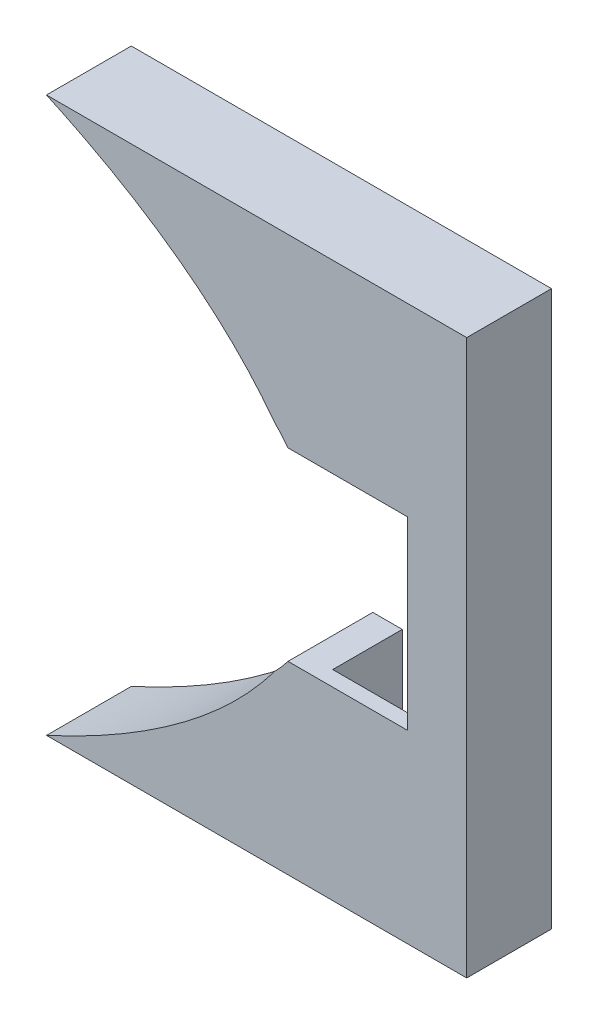
SolidWorks part; units mm, degrees
ref_plane "Front Plane" through (0, 0, 0) normal (0, 0, 1) x (1, 0, 0)
ref_plane "Top Plane" through (0, 0, 0) normal (0, 1, 0) x (1, 0, 0)
ref_plane "Right Plane" through (0, 0, 0) normal (1, 0, 0) x (0, 0, -1)
sketch "Sketch1" plane through (0, 0, 0) normal (0, 0, 1) x (1, 0, 0)
  line L0 (61.5951, 0) -> (57.3248, 0) construction
  line L1 (-2.6813, 23.8497) -> (-2.6813, -23.8497)
  line L2 (-2.6813, 23.8497) -> (-2.6813, -23.8497)
  line L3 (60.35, 4.95) -> (60.85, 4.95) construction
  line L4 (60.85, 5.45) -> (55.8, 5.45)
  line L5 (60.85, 5.45) -> (60.85, -5.45)
  line L6 (60.85, -5.45) -> (55.8, -5.45)
  line L7 (55.8, 5.45) -> (55.8, -5.45)
  line L8 (60.85, 5.45) -> (55.8, -5.45) construction
  line L9 (60.85, -5.45) -> (55.8, 5.45) construction
  line L10 (60.35, 4.95) -> (60.35, 5.45) construction
  line L11 (55.8, 5.45) -> (54.0622, 5.45)
  line L12 (55.8, -14.85) -> (63.1, 14.85) construction
  line L13 (63.1, 14.85) -> (64.6, 14.85) construction
  line L14 (54.3, -16.35) -> (64.6, -16.35)
  line L15 (54.3, -16.35) -> (54.3, 16.35)
  line L16 (54.3, 16.35) -> (64.6, 16.35)
  line L17 (64.6, -16.35) -> (64.6, 16.35)
  line L18 (54.3, -16.35) -> (64.6, 16.35) construction
  line L19 (54.3, 16.35) -> (64.6, -16.35) construction
  line L20 (63.1, 14.85) -> (63.1, 16.35) construction
  line L21 (54.3, 16.35) -> (39.8224, 16.35)
  line L22 (55.8, 14.85) -> (55.8, 4.95)
  line L23 (55.8, 4.95) -> (59.2, 4.95)
  line L24 (59.2, 4.95) -> (60.35, 4.95)
  line L25 (60.35, 4.95) -> (60.35, -4.95)
  line L26 (60.35, -4.95) -> (59.2, -4.95)
  line L27 (59.2, -4.95) -> (55.8, -4.95)
  line L28 (55.8, -4.95) -> (55.8, -14.85)
  line L29 (55.8, -14.85) -> (63.1, -14.85)
  line L30 (63.1, -14.85) -> (63.1, 14.85)
  line L31 (63.1, 14.85) -> (55.8, 14.85)
  line L32 (55.8, 14.85) -> (55.8, 4.95)
  line L33 (55.8, 4.95) -> (59.2, 4.95)
  line L34 (59.2, 4.95) -> (60.35, 4.95)
  line L35 (60.35, 4.95) -> (60.35, -4.95)
  line L36 (60.35, -4.95) -> (59.2, -4.95)
  line L37 (59.2, -4.95) -> (55.8, -4.95)
  line L38 (55.8, -4.95) -> (55.8, -14.85)
  line L39 (55.8, -14.85) -> (63.1, -14.85)
  line L40 (63.1, -14.85) -> (63.1, 14.85)
  line L41 (63.1, 14.85) -> (55.8, 14.85)
  line L42 (54.3, -16.35) -> (39.8224, -16.35)
  line L43 (55.8, -5.45) -> (54.0622, -5.45)
  line L44 (55.8, 4.95) -> (54.3, 4.95)
  line L45 (55.8, 4.95) -> (55.8, -4.95)
  line L46 (55.8, -4.95) -> (54.3, -4.95)
  line L47 (54.3, 4.95) -> (54.3, -4.95)
  arc A1 (53.264, -6.364) -> (53.264, 6.364) centre (46.9, 0) ccw
  arc A2 (53.264, -6.364) -> (53.264, 6.364) centre (46.9, 0) ccw
  spline S2 degree 3 poles (-2788.5351, -933.1128) (3254.9192, 628.8908) (-3260.7685, -317.1067) (2992.5839, 170.8336) knots -3.563477 -3.563477 -3.563477 -3.563477 4.61246 4.61246 4.61246 4.61246 only from (53.264, 6.364) to (-2.6813, 23.8497)
  spline S3 degree 3 poles (2992.541, -170.8303) (-3260.7166, 317.1006) (3254.8593, -628.8806) (-2788.4709, 933.0962) knots -3.612441 -3.612441 -3.612441 -3.612441 4.563448 4.563448 4.563448 4.563448 only from (-2.6813, -23.8497) to (53.264, -6.364)
  spline S4 degree 3 poles (53.264, 6.364) (41.9045, 21.6052) (7.8082, 25.0296) (-2.6813, 23.8497) knots 0 0 0 0 1 1 1 1
  spline S5 degree 3 poles (-2.6813, -23.8497) (7.8082, -25.0296) (41.9045, -21.6052) (53.264, -6.364) knots 0 0 0 0 1 1 1 1
  point P2 (59.45, 0)
  point P28 (58.325, 0)
  dimension "D3" = 1.5
  dimension "D4" = 0.5
  dimension "D1" = 0
  dimension "D2" = 0.1
extrude "Boss-Extrude1" add sketch "Sketch1" against normal blind 3.3 contours S4 A2 L15 L21 | A2 L44 L32 L41 L40 L39 L38 L46 L15 L14 L17 L16 | S5 L42 L15 A2
sketch "Sketch2" plane through (0, 0, 0) normal (0, 0, -1) x (-1, 0, 0)
  line L0 (-63.1, -14.85) -> (-63.1, 14.85) construction
  line L1 (-55.8, 14.85) -> (-63.1, 14.85)
  line L2 (-55.8, 14.85) -> (-55.8, 5.45)
  line L3 (-55.8, 5.45) -> (-63.1, 5.45)
  line L4 (-63.1, 14.85) -> (-63.1, 5.45)
  line L6 (-64.6, 0) -> (-63.1, 0) construction
  line L7 (-64.6, -16.35) -> (-64.6, 16.35) construction
  line L8 (-55.8, -14.85) -> (-55.8, -5.45)
  line L9 (-55.8, -14.85) -> (-63.1, -14.85)
  line L10 (-63.1, -14.85) -> (-63.1, -5.45)
  line L11 (-55.8, -5.45) -> (-63.1, -5.45)
  line L12 (-55.8, 5.45) -> (-54.0622, 5.45) construction
  line L14 (-63.1, -5.45) -> (-61.1, -5.45)
  line L15 (-63.1, -5.45) -> (-63.1, 5.45)
  line L16 (-63.1, 5.45) -> (-61.1, 5.45)
  line L17 (-61.1, -5.45) -> (-61.1, 5.45)
  line M27 (-55.8, 5.45) -> (-55.8, 14.85)
  line M28 (-55.8, 14.85) -> (-63.1, 14.85)
  line M29 (-63.1, 14.85) -> (-63.1, -14.85)
  line M30 (-63.1, -14.85) -> (-55.8, -14.85)
  line M31 (-55.8, -14.85) -> (-55.8, -5.45)
  dimension "D1" = 2
extrude "Boss-Extrude2" add sketch "Sketch2" along normal blind 0.9 contours L11 M31 M30 M29 | L3 M27 M29 M28 | L17 L11 L15 L3 M29
sketch "Sketch3" plane through (0, 0, -3.3) normal (0, 0, 1) x (1, 0, 0)
  line L0 (63.3, 15.05) -> (64.6, 15.05)
  line L1 (63.3, -15.05) -> (64.6, -15.05)
  line L8 (61.1, 5.45) -> (61.1, -5.45)
  line L9 (61.1, 5.45) -> (61.1, -5.45)
  line L10 (54.0622, 5.45) -> (61.1, 5.45)
  line L14 (54.0622, 5.45) -> (61.1, 5.45)
  line L17 (39.8224, -16.35) -> (64.6, -16.35)
  line L18 (64.6, -16.35) -> (64.6, 16.35)
  line L19 (64.6, 16.35) -> (39.8224, 16.35)
  line L27 (39.8224, -16.35) -> (64.6, -16.35)
  line L28 (64.6, -16.35) -> (64.6, 16.35)
  line L29 (64.6, 16.35) -> (39.8224, 16.35)
  line L30 (61.1, -5.45) -> (54.0622, -5.45)
  line L31 (61.1, -5.45) -> (54.0622, -5.45)
  arc A2 (54.0622, 5.45) -> (53.264, 6.364) centre (46.9, 0) ccw
  arc A3 (53.264, -6.364) -> (54.0622, -5.45) centre (46.9, 0) ccw
  arc A4 (54.0622, 5.45) -> (53.264, 6.364) centre (46.9, 0) ccw
  arc A5 (53.264, -6.364) -> (54.0622, -5.45) centre (46.9, 0) ccw
  spline S2 degree 3 poles (2037.6541, 100.271) (-2259.1717, -196.4273) (2247.1276, 446.4623) (-1822.1953, -675.7926) knots -3.870469 -3.870469 -3.870469 -3.870469 3.340755 3.340755 3.340755 3.340755 only from (39.8224, 16.35) to (53.264, 6.364)
  spline S3 degree 3 poles (-1822.219, 675.7991) (2247.1474, -446.4655) (-2259.185, 196.4286) (2037.6612, -100.2715) knots -2.340769 -2.340769 -2.340769 -2.340769 4.870473 4.870473 4.870473 4.870473 only from (53.264, -6.364) to (39.8224, -16.35)
  spline S4 degree 3 poles (39.8224, 16.35) (45.3686, 13.804) (50.1633, 10.5242) (53.264, 6.364) knots 0 0 0 0 0.272958 0.272958 0.272958 0.272958
  spline S5 degree 3 poles (53.264, -6.364) (50.1633, -10.5242) (45.3686, -13.804) (39.8224, -16.35) knots 0.727042 0.727042 0.727042 0.727042 1 1 1 1
  dimension "D1" = 0
extrude "Boss-Extrude3" add sketch "Sketch3" against normal offset from surface (1.7 mm away) 5
